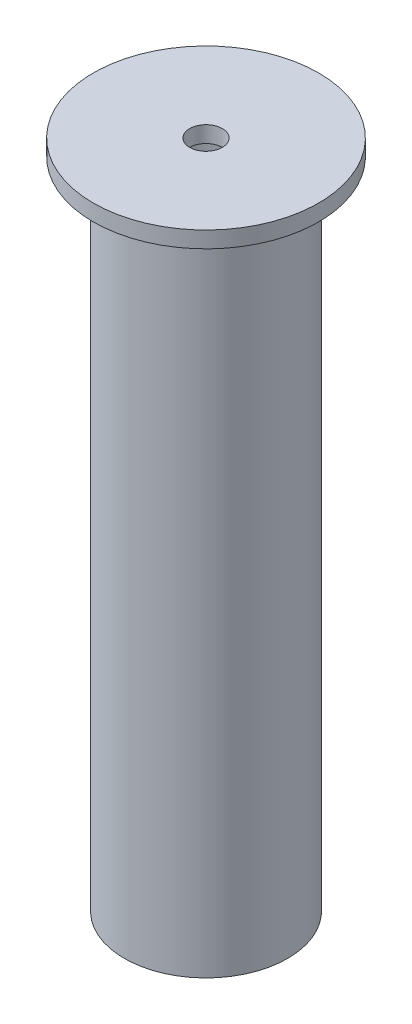
SolidWorks part; units mm, degrees
ref_plane "Plano frontal" through (0, 0, 0) normal (0, 0, 1) x (1, 0, 0)
ref_plane "Plano superior" through (0, 0, 0) normal (0, 1, 0) x (1, 0, 0)
ref_plane "Plano direito" through (0, 0, 0) normal (1, 0, 0) x (0, 0, -1)
sketch "Esboço1" plane through (0, 0, 0) normal (0, 0, 1) x (1, 0, 0)
  line L0 (0, 0) -> (0, 410) construction
  line L1 (0, 0) -> (215.8131, 0) construction
  line L2 (10, 410) -> (69, 410)
  line L3 (69, 410) -> (69, 400)
  line L4 (50, 0) -> (38, 0)
  line L5 (38, 0) -> (38, 10)
  line L6 (38, 10) -> (44, 10)
  line L7 (44, 10) -> (44, 400)
  line L8 (44, 400) -> (10, 400)
  line L10 (69, 400) -> (50, 400)
  line L11 (50, 400) -> (50, 0)
  line L12 (10, 410) -> (10, 400)
  dimension "D1" = 6
  dimension "D2" = 10
  dimension "D3" = 6
  dimension "D4" = 10
  dimension "D5" = 138
  dimension "D6" = 400
  dimension "D7" = 100
  dimension "D8" = 20
revolve "Revolução1" add sketch "Esboço1" angle 360 about L0
